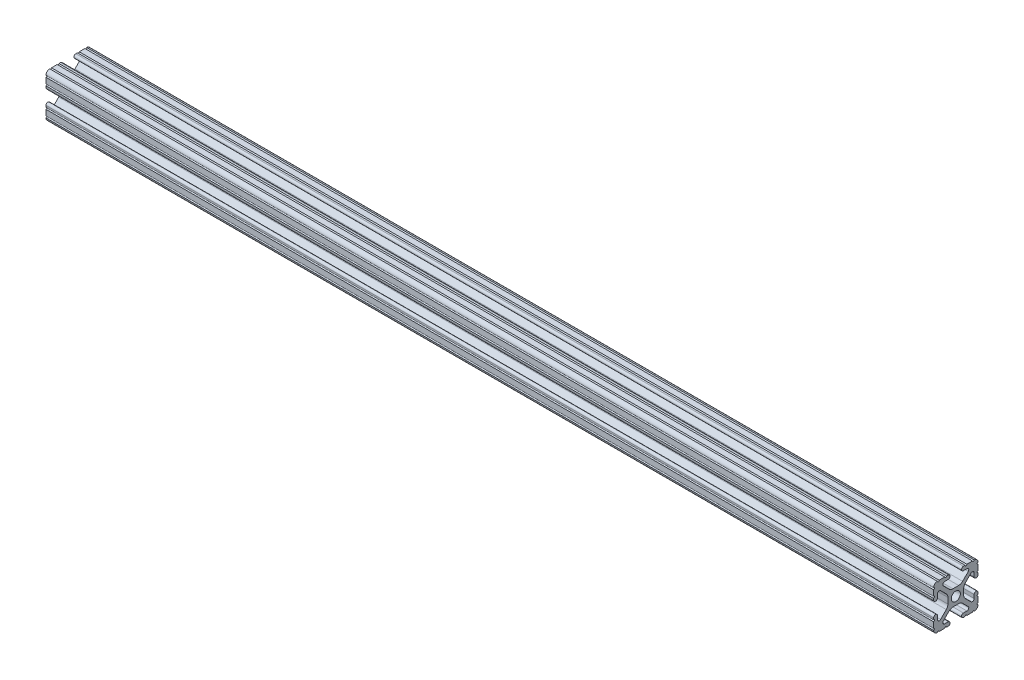
SolidWorks part; units mm, degrees
ref_plane "Front Plane" through (0, 0, 0) normal (0, 0, 1) x (1, 0, 0)
ref_plane "Top Plane" through (0, 0, 0) normal (0, 1, 0) x (1, 0, 0)
ref_plane "Right Plane" through (0, 0, 0) normal (1, 0, 0) x (0, 0, -1)
sketch "Sketch1" plane through (0, 0, 0) normal (0, 0, 1) x (1, 0, 0)
  line L0 (-254, 0) -> (254, 0)
  point P2 (0, 0)
  dimension "D1" = 508
other "Fractional 1010(1)"
ref_plane "Plane1" through (-254, 0, 0) normal (1, 0, 0) x (0, 1, 0)
sketch "Sketch11" plane through (-254, 0, 0) normal (1, 0, 0) x (0, 1, 0)
  line L0 (10.5918, 12.7) -> (10.5664, 12.7)
  line L1 (9.5504, 12.7) -> (6.3246, 12.7)
  line L2 (5.3086, 12.7) -> (4.3561, 12.7)
  line L3 (4.3561, 10.4902) -> (6.3701, 10.4902)
  line L4 (7.1192, 8.6817) -> (3.8846, 5.4471)
  line L5 (1.6396, 4.5172) -> (-1.6396, 4.5172)
  line L6 (-3.8846, 5.4471) -> (-7.1192, 8.6817)
  line L7 (-6.3701, 10.4902) -> (-4.3561, 10.4902)
  line L8 (-4.3561, 12.7) -> (-5.3086, 12.7)
  line L9 (-6.3246, 12.7) -> (-9.5504, 12.7)
  line L10 (-10.5664, 12.7) -> (-10.5918, 12.7)
  line L11 (-12.7, 10.5918) -> (-12.7, 10.5664)
  line L12 (-12.7, 9.5504) -> (-12.7, 6.3246)
  line L13 (-12.7, 5.3086) -> (-12.7, 4.3561)
  line L14 (-10.4902, 4.3561) -> (-10.4902, 6.3701)
  line L15 (-8.6817, 7.1192) -> (-5.4471, 3.8846)
  line L16 (-4.5172, 1.6396) -> (-4.5172, -1.6396)
  line L17 (-5.4471, -3.8846) -> (-8.6817, -7.1192)
  line L18 (-10.4902, -6.3701) -> (-10.4902, -4.3561)
  line L19 (-12.7, -4.3561) -> (-12.7, -5.3086)
  line L20 (-12.7, -6.3246) -> (-12.7, -9.5504)
  line L21 (-12.7, -10.5664) -> (-12.7, -10.5918)
  line L22 (-10.5918, -12.7) -> (-10.5664, -12.7)
  line L23 (-9.5504, -12.7) -> (-6.3246, -12.7)
  line L24 (-5.3086, -12.7) -> (-4.3561, -12.7)
  line L25 (-4.3561, -10.4902) -> (-6.3701, -10.4902)
  line L26 (-7.1192, -8.6817) -> (-3.8846, -5.4471)
  line L27 (-1.6396, -4.5172) -> (1.6396, -4.5172)
  line L28 (3.8846, -5.4471) -> (7.1192, -8.6817)
  line L29 (6.3701, -10.4902) -> (4.3561, -10.4902)
  line L30 (4.3561, -12.7) -> (5.3086, -12.7)
  line L31 (6.3246, -12.7) -> (9.5504, -12.7)
  line L32 (10.5664, -12.7) -> (10.5918, -12.7)
  line L33 (12.7, -10.5918) -> (12.7, -10.5664)
  line L34 (12.7, -9.5504) -> (12.7, -6.3246)
  line L35 (12.7, -5.3086) -> (12.7, -4.3561)
  line L36 (10.4902, -4.3561) -> (10.4902, -6.3701)
  line L37 (8.6817, -7.1192) -> (5.4471, -3.8846)
  line L38 (4.5172, -1.6396) -> (4.5172, 1.6396)
  line L39 (5.4471, 3.8846) -> (8.6817, 7.1192)
  line L40 (10.4902, 6.3701) -> (10.4902, 4.3561)
  line L41 (12.7, 4.3561) -> (12.7, 5.3086)
  line L42 (12.7, 6.3246) -> (12.7, 9.5504)
  line L43 (12.7, 10.5664) -> (12.7, 10.5918)
  circle A0 centre (0, 0) radius 2.6035
  arc A1 (12.7, 10.5918) -> (10.5918, 12.7) centre (10.5918, 10.5918) ccw
  arc A2 (9.5504, 12.7) -> (10.5664, 12.7) centre (10.0584, 12.7) ccw
  arc A3 (5.3086, 12.7) -> (6.3246, 12.7) centre (5.8166, 12.7) ccw
  arc A4 (4.3561, 12.7) -> (4.3561, 10.4902) centre (4.3561, 11.5951) ccw
  arc A5 (7.1192, 8.6817) -> (6.3701, 10.4902) centre (6.3701, 9.4308) ccw
  arc A6 (1.6396, 4.5172) -> (3.8846, 5.4471) centre (1.6396, 7.6922) ccw
  arc A7 (-3.8846, 5.4471) -> (-1.6396, 4.5172) centre (-1.6396, 7.6922) ccw
  arc A8 (-6.3701, 10.4902) -> (-7.1192, 8.6817) centre (-6.3701, 9.4308) ccw
  arc A9 (-4.3561, 10.4902) -> (-4.3561, 12.7) centre (-4.3561, 11.5951) ccw
  arc A10 (-6.3246, 12.7) -> (-5.3086, 12.7) centre (-5.8166, 12.7) ccw
  arc A11 (-10.5664, 12.7) -> (-9.5504, 12.7) centre (-10.0584, 12.7) ccw
  arc A12 (-10.5918, 12.7) -> (-12.7, 10.5918) centre (-10.5918, 10.5918) ccw
  arc A13 (-12.7, 9.5504) -> (-12.7, 10.5664) centre (-12.7, 10.0584) ccw
  arc A14 (-12.7, 5.3086) -> (-12.7, 6.3246) centre (-12.7, 5.8166) ccw
  arc A15 (-12.7, 4.3561) -> (-10.4902, 4.3561) centre (-11.5951, 4.3561) ccw
  arc A16 (-8.6817, 7.1192) -> (-10.4902, 6.3701) centre (-9.4308, 6.3701) ccw
  arc A17 (-4.5172, 1.6396) -> (-5.4471, 3.8846) centre (-7.6922, 1.6396) ccw
  arc A18 (-5.4471, -3.8846) -> (-4.5172, -1.6396) centre (-7.6922, -1.6396) ccw
  arc A19 (-10.4902, -6.3701) -> (-8.6817, -7.1192) centre (-9.4308, -6.3701) ccw
  arc A20 (-10.4902, -4.3561) -> (-12.7, -4.3561) centre (-11.5951, -4.3561) ccw
  arc A21 (-12.7, -6.3246) -> (-12.7, -5.3086) centre (-12.7, -5.8166) ccw
  arc A22 (-12.7, -10.5664) -> (-12.7, -9.5504) centre (-12.7, -10.0584) ccw
  arc A23 (-12.7, -10.5918) -> (-10.5918, -12.7) centre (-10.5918, -10.5918) ccw
  arc A24 (-9.5504, -12.7) -> (-10.5664, -12.7) centre (-10.0584, -12.7) ccw
  arc A25 (-5.3086, -12.7) -> (-6.3246, -12.7) centre (-5.8166, -12.7) ccw
  arc A26 (-4.3561, -12.7) -> (-4.3561, -10.4902) centre (-4.3561, -11.5951) ccw
  arc A27 (-7.1192, -8.6817) -> (-6.3701, -10.4902) centre (-6.3701, -9.4308) ccw
  arc A28 (-1.6396, -4.5172) -> (-3.8846, -5.4471) centre (-1.6396, -7.6922) ccw
  arc A29 (3.8846, -5.4471) -> (1.6396, -4.5172) centre (1.6396, -7.6922) ccw
  arc A30 (6.3701, -10.4902) -> (7.1192, -8.6817) centre (6.3701, -9.4308) ccw
  arc A31 (4.3561, -10.4902) -> (4.3561, -12.7) centre (4.3561, -11.5951) ccw
  arc A32 (6.3246, -12.7) -> (5.3086, -12.7) centre (5.8166, -12.7) ccw
  arc A33 (10.5664, -12.7) -> (9.5504, -12.7) centre (10.0584, -12.7) ccw
  arc A34 (10.5918, -12.7) -> (12.7, -10.5918) centre (10.5918, -10.5918) ccw
  arc A35 (12.7, -9.5504) -> (12.7, -10.5664) centre (12.7, -10.0584) ccw
  arc A36 (12.7, -5.3086) -> (12.7, -6.3246) centre (12.7, -5.8166) ccw
  arc A37 (12.7, -4.3561) -> (10.4902, -4.3561) centre (11.5951, -4.3561) ccw
  arc A38 (8.6817, -7.1192) -> (10.4902, -6.3701) centre (9.4308, -6.3701) ccw
  arc A39 (4.5172, -1.6396) -> (5.4471, -3.8846) centre (7.6922, -1.6396) ccw
  arc A40 (5.4471, 3.8846) -> (4.5172, 1.6396) centre (7.6922, 1.6396) ccw
  arc A41 (10.4902, 6.3701) -> (8.6817, 7.1192) centre (9.4308, 6.3701) ccw
  arc A42 (10.4902, 4.3561) -> (12.7, 4.3561) centre (11.5951, 4.3561) ccw
  arc A43 (12.7, 6.3246) -> (12.7, 5.3086) centre (12.7, 5.8166) ccw
  arc A44 (12.7, 10.5664) -> (12.7, 9.5504) centre (12.7, 10.0584) ccw
  point P0 (0, 0)
